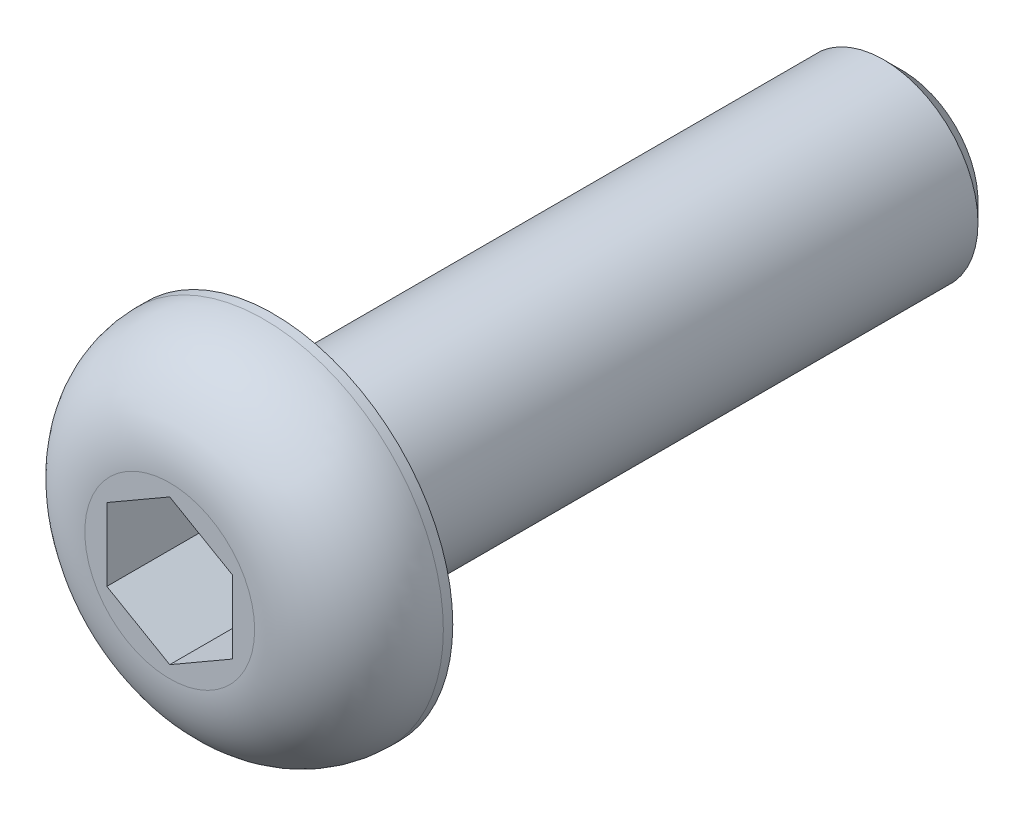
SolidWorks part; units mm, degrees
ref_plane "Front Plane" through (0, 0, 0) normal (0, 0, 1) x (1, 0, 0)
ref_plane "Top Plane" through (0, 0, 0) normal (0, 1, 0) x (1, 0, 0)
ref_plane "Right Plane" through (0, 0, 0) normal (1, 0, 0) x (0, 0, -1)
sketch "Sketch1" plane through (0, 0, 0) normal (0, 0, 1) x (1, 0, 0)
  circle A0 centre (0, 0) radius 2.85
  dimension "D1" = 5.7
extrude "Boss-Extrude1" add sketch "Sketch1" along normal blind 1.65
sketch "Sketch2" plane through (0, 0, 0) normal (0, 0, -1) x (-1, 0, 0)
  circle A0 centre (0, 0) radius 1.5
  dimension "D1" = 3
extrude "Boss-Extrude2" add sketch "Sketch2" along normal blind 10
chamfer "Chamfer1" distance 0.3 angle 45 1 edges at (-1.5, 0, -10)
sketch "Sketch3" plane through (0, 0, 1.65) normal (0, 0, 1) x (1, 0, 0)
  line L1 (0, 1.1547) -> (-1, 0.5774)
  line L2 (-1, 0.5774) -> (-1, -0.5774)
  line L3 (-1, -0.5774) -> (0, -1.1547)
  line L4 (0, -1.1547) -> (1, -0.5774)
  line L5 (1, -0.5774) -> (1, 0.5774)
  line L6 (1, 0.5774) -> (0, 1.1547)
  circle A0 centre (0, 0) radius 1 construction
  dimension "D1" = 2
extrude "Cut-Extrude1" cut sketch "Sketch3" against normal blind 2
fillet "Fillet1" radius 1.5 1 edges at (2.85, 0, 1.65)
